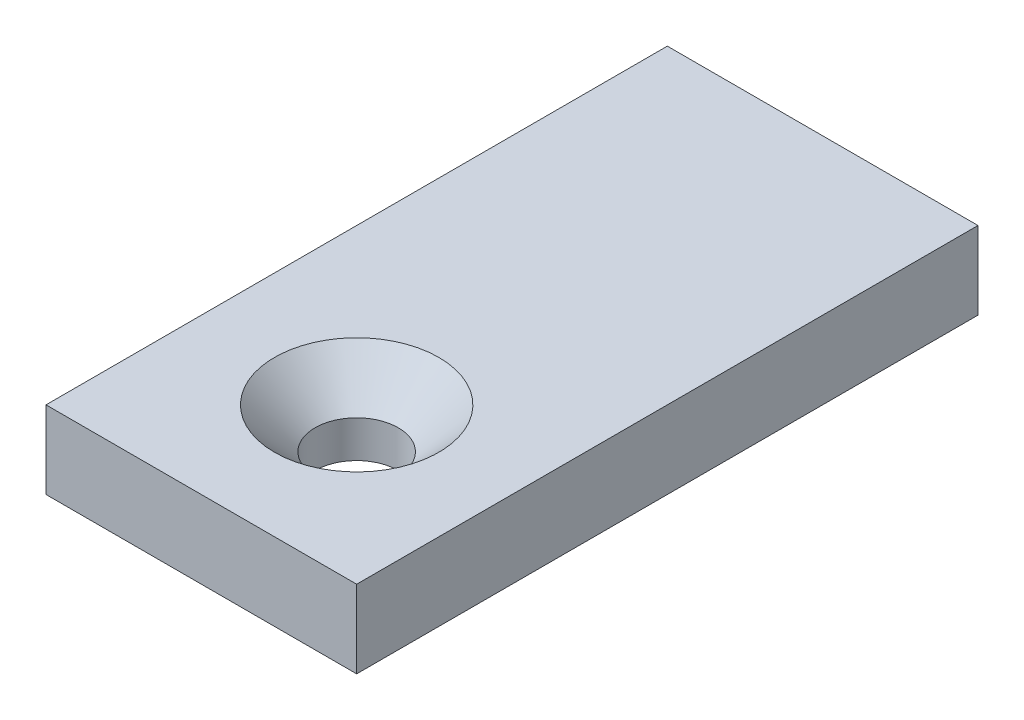
SolidWorks part; units mm, degrees
material "Copper"
ref_plane "Front Plane" through (0, 0, 0) normal (0, 0, 1) x (1, 0, 0)
ref_plane "Top Plane" through (0, 0, 0) normal (0, 1, 0) x (1, 0, 0)
ref_plane "Right Plane" through (0, 0, 0) normal (1, 0, 0) x (0, 0, -1)
sketch "Sketch1" plane through (0, 0, 0) normal (0, 0, 1) x (1, 0, 0)
  line L0 (0, 0) -> (12.7, 0)
  dimension "D1" = 12.7
sketch "Sketch9" plane through (0, 0, 0) normal (0, 1, 0) x (1, 0, 0)
  line L1 (0, 0) -> (12.7, 0)
  line L2 (0, 0) -> (0, 25.4)
  line L3 (0, 25.4) -> (12.7, 25.4)
  line L4 (12.7, 0) -> (12.7, 25.4)
  dimension "D1" = 12.7
  dimension "D2" = 25.4
extrude "Boss-Extrude1" add sketch "Sketch9" along normal blind 3.175
hole_wizard "CSK for M3 SFHCS2" positions "Sketch11" profile "Sketch10" countersink size "M3" standard "ANSI Metric" end condition through all
sketch "Sketch11" plane through (0, 3.175, 0) normal (0, 1, 0) x (1, 0, 0)
  line L0 (0, 0) -> (12.7, 0) construction
  point P0 (6.35, 6.35)
  point P5 (6.35, 0)
  dimension "D1" = 6.35
sketch "Sketch10" plane through (6.35, 3.175, -6.35) normal (1, 0, 0) x (0, 0, 1)
  line L0 (0, 0) -> (0, 3.175)
  line L1 (0, 3.175) -> (1.7, 3.175)
  line L2 (1.7, 3.175) -> (1.7, 1.66)
  line L3 (1.7, 1.66) -> (3.36, 0)
  line L5 (3.36, 0) -> (0, 0)
  line L6 (-1.7, 1.66) -> (-3.36, 0) construction
  line L11 (0, -6.35) -> (0, 107.95) construction
  dimension "Thru Hole Dia." = 3.4
  dimension "Thru Hole Depth" = 3.175
  dimension "Near C'Sink Dia." = 6.72
  dimension "Near C'Sink Angle" = 90
equation "\"ABS_thickness\" = 1.59\t"
equation "\"ABS_thickness_1/8\" = 3.175\t"
equation "\"Bus_bar_thickness\" = 3.175"
equation "\"Connector_width\" = 20.2"
equation "\"Number_of_cells_long\" = 25"
equation "\"Number_of_cells_wide\" = 2"
equation "\"Cell_height\" = 65.0"
equation "\"Cell_diam\" = 18.0"
equation "\"D1@Boss-Extrude1\"=\"Bus_bar_thickness\""
